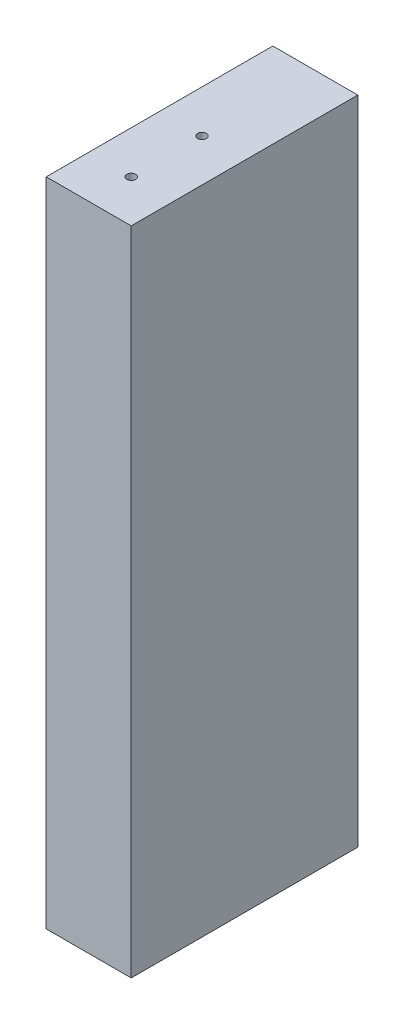
SolidWorks part; units mm, degrees
material "MDF"
ref_plane "Front" through (0, 0, 0) normal (0, 0, 1) x (1, 0, 0)
ref_plane "Top" through (0, 0, 0) normal (0, 1, 0) x (1, 0, 0)
ref_plane "Right" through (0, 0, 0) normal (1, 0, 0) x (0, 0, -1)
sketch "Sketch1" plane through (0, 0, 0) normal (0, 0, 1) x (1, 0, 0)
  line L0 (487.3718, 6431.28) -> (273.05, 6431.28) construction
  line L1 (462.7063, 6285.23) -> (481.7563, 6285.23)
  line L2 (462.7063, 6285.23) -> (462.7063, 6431.28)
  line L3 (462.7063, 6431.28) -> (481.7563, 6431.28)
  line L4 (481.7563, 6285.23) -> (481.7563, 6431.28)
  dimension "D1" = 19.05
extrude "Boss-Extrude1" add sketch "Sketch1" along normal blind 50.8
hole_wizard "5/64 (0.07813) Diameter Hole1" positions "Sketch2" profile "Sketch3" hole size "5/64" standard "ANSI Inch"
sketch "Sketch2" plane through (0, 0, -19.0501) normal (0, 0, -1) x (-1, 0, 0)
  point P0 (-481.5892, 6993.255)
  point P9 (-386.3392, 6993.255)
  point P18 (-291.0892, 6993.255)
  point P21 (-295.275, 6965.1359)
  point P33 (-295.275, 6812.7359)
  point P45 (-295.275, 6660.3359)
  point P48 (-285.1664, 6631.4688)
  point P66 (-475.4773, 6631.4688)
  point P69 (-485.0023, 6660.3359)
  point P81 (-485.0023, 6812.7359)
  point P93 (-485.0023, 6965.1359)
  point P96 (-478.3656, 6611.6708)
  point P114 (-287.8656, 6611.6708)
  point P117 (-307.975, 6564.3379)
  point P127 (-307.975, 6488.1379)
  point P130 (-284.9609, 6440.805)
  point P143 (-380.2109, 6440.805)
  point P152 (-475.4609, 6440.805)
  point P155 (-446.8313, 6488.1379)
  point P161 (-446.8313, 6564.3379)
  point P164 (-472.2313, 6396.355)
  point P170 (-472.2313, 6320.155)
  point P173 (-472.6532, 6275.705)
  point P182 (-377.4032, 6275.705)
  point P191 (-282.1532, 6275.705)
  point P194 (-282.575, 6320.155)
  point P200 (-282.575, 6396.355)
  point P203 (-435.5986, 6221.73)
  point P209 (-435.5986, 6145.53)
  point P233 (-450.5925, 6091.555)
  point P242 (-460.9986, 6091.5555)
  point P245 (-460.9986, 6056.63)
  point P251 (-460.9986, 5980.43)
  point P263 (-460.9986, 5945.505)
  point P280 (-282.1532, 5945.505)
  point P284 (-368.6118, 5945.505)
sketch "Sketch3" plane through (481.5892, 6993.255, -19.0501) normal (1, 0, 0) x (0, 1, 0)
  line L0 (0, 0) -> (0, 38.6962)
  line L1 (0, 38.6962) -> (0.9923, 38.1)
  line L2 (0.9923, 38.1) -> (0.9923, 0)
  line L3 (0.9923, 0) -> (0, 0)
  line L4 (0, 38.6962) -> (-0.9923, 38.1) construction
  line L5 (0, -6.35) -> (0, 107.95) construction
  dimension "Hole Dia." = 1.9845
  dimension "Hole Depth" = 38.1
  dimension "Drill Angle" = 118
hole_wizard "5/64 (0.07813) Diameter Hole2" positions "Sketch4" profile "Sketch5" hole size "5/64" standard "ANSI Inch"
sketch "Sketch4" plane through (189.6563, 0, -19.0501) normal (0, 0, -1) x (-1, 0, 0)
  point P0 (-481.5892, 6993.255)
  point P9 (-386.3392, 6993.255)
  point P18 (-291.0892, 6993.255)
  point P21 (-295.275, 6965.1359)
  point P33 (-295.275, 6812.7359)
  point P45 (-295.275, 6660.3359)
  point P48 (-285.1664, 6631.4688)
  point P66 (-475.4773, 6631.4688)
  point P69 (-485.0023, 6660.3359)
  point P81 (-485.0023, 6812.7359)
  point P93 (-485.0023, 6965.1359)
  point P96 (-478.3656, 6611.6708)
  point P114 (-287.8656, 6611.6708)
  point P117 (-307.975, 6564.3379)
  point P127 (-307.975, 6488.1379)
  point P130 (-284.9609, 6440.805)
  point P143 (-380.2109, 6440.805)
  point P152 (-475.4609, 6440.805)
  point P155 (-446.8313, 6488.1379)
  point P161 (-446.8313, 6564.3379)
  point P164 (-472.2313, 6396.355)
  point P170 (-472.2313, 6320.155)
  point P173 (-472.6532, 6275.705)
  point P182 (-377.4032, 6275.705)
  point P191 (-282.1532, 6275.705)
  point P194 (-282.575, 6320.155)
  point P200 (-282.575, 6396.355)
  point P203 (-435.5986, 6221.73)
  point P209 (-435.5986, 6145.53)
  point P233 (-450.5925, 6091.555)
  point P242 (-460.9986, 6091.5555)
  point P245 (-460.9986, 6056.63)
  point P251 (-460.9986, 5980.43)
  point P263 (-460.9986, 5945.505)
  point P280 (-282.1532, 5945.505)
  point P284 (-368.6118, 5945.505)
sketch "Sketch5" plane through (671.2456, 6993.255, -19.0501) normal (1, 0, 0) x (0, 1, 0)
  line L0 (0, 0) -> (0, 38.6962)
  line L1 (0, 38.6962) -> (0.9923, 38.1)
  line L2 (0.9923, 38.1) -> (0.9923, 0)
  line L3 (0.9923, 0) -> (0, 0)
  line L4 (0, 38.6962) -> (-0.9923, 38.1) construction
  line L5 (0, -6.35) -> (0, 107.95) construction
  dimension "Hole Dia." = 1.9845
  dimension "Hole Depth" = 38.1
  dimension "Drill Angle" = 118
hole_wizard "5/64 (0.07813) Diameter Hole3" positions "Sketch6" profile "Sketch7" hole size "5/64" standard "ANSI Inch"
sketch "Sketch6" plane through (0, 6431.28, 0) normal (0, 1, 0) x (1, 0, 0)
  line L0 (472.2313, -50.8) -> (472.2313, 0) construction
  line L1 (481.7563, -50.8) -> (462.7063, -50.8) construction
  line L2 (481.7563, 0) -> (462.7063, 0) construction
  point P9 (472.2313, -25.4)
  point P11 (472.2313, -41.275)
  dimension "D1" = 15.875
sketch "Sketch7" plane through (472.2313, 6431.28, 41.275) normal (1, 0, 0) x (0, 0, 1)
  line L0 (0, 0) -> (0, 19.6462)
  line L1 (0, 19.6462) -> (0.9923, 19.05)
  line L2 (0.9923, 19.05) -> (0.9923, 0)
  line L5 (0.9923, 0) -> (0, 0)
  line L10 (0, 19.6462) -> (-0.9923, 19.05) construction
  line L11 (0, -6.35) -> (0, 107.95) construction
  dimension "Hole Dia." = 1.9845
  dimension "Hole Depth" = 19.05
  dimension "Drill Angle" = 118
hole_wizard "5/64 (0.07813) Diameter Hole4" positions "Sketch8" profile "Sketch9" hole size "5/64" standard "ANSI Inch"
sketch "Sketch8" plane through (0, 6285.23, 0) normal (0, -1, 0) x (-1, 0, 0)
  circle A0 centre (-472.2313, -41.275) radius 0.9923 construction
  circle A1 centre (-472.2313, -25.4) radius 0.9923 construction
  point P0 (-472.2313, -25.4)
  point P2 (-472.2313, -41.275)
sketch "Sketch9" plane through (472.2313, 6285.23, 25.4) normal (1, 0, 0) x (0, 0, -1)
  line L0 (0, 0) -> (0, 19.6462)
  line L1 (0, 19.6462) -> (0.9923, 19.05)
  line L2 (0.9923, 19.05) -> (0.9923, 0)
  line L5 (0.9923, 0) -> (0, 0)
  line L10 (0, 19.6462) -> (-0.9923, 19.05) construction
  line L11 (0, -6.35) -> (0, 107.95) construction
  dimension "Hole Dia." = 1.9845
  dimension "Hole Depth" = 19.05
  dimension "Drill Angle" = 118
